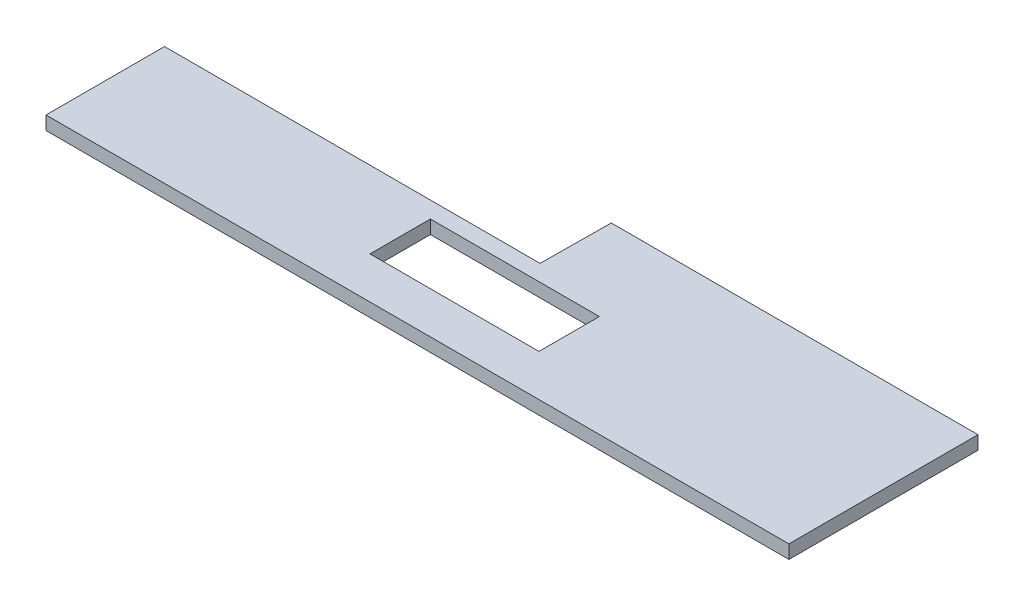
SolidWorks part; units mm, degrees
ref_plane "Front Plane" through (0, 0, 0) normal (0, 0, 1) x (1, 0, 0)
ref_plane "Top Plane" through (0, 0, 0) normal (0, 1, 0) x (1, 0, 0)
ref_plane "Right Plane" through (0, 0, 0) normal (1, 0, 0) x (0, 0, -1)
sketch "Sketch1" plane through (0, 0, 0) normal (0, 1, 0) x (1, 0, 0)
  line L1 (12.2447, 9.2899) -> (66.5437, 9.2899)
  line L2 (-43.4563, -1.1624) -> (-43.4563, -18.7101)
  line L3 (-43.4563, -18.7101) -> (66.5437, -18.7101)
  line L4 (66.5437, 9.2899) -> (66.5437, -18.7101)
  line L5 (12.2447, 9.2899) -> (12.1483, -1.1624)
  line L6 (12.1483, -1.1624) -> (-43.4563, -1.1624)
  line L7 (-1.6544, -3.5927) -> (23.3583, -3.5927)
  line L8 (-1.6544, -3.5927) -> (-1.6544, -12.5347)
  line L9 (-1.6544, -12.5347) -> (23.3583, -12.5347)
  line L10 (23.3583, -3.5927) -> (23.3583, -12.5347)
  point P0 (12.1483, -1.1624)
  dimension "D2" = 28
extrude "Boss-Extrude1" add sketch "Sketch1" along normal blind 2
